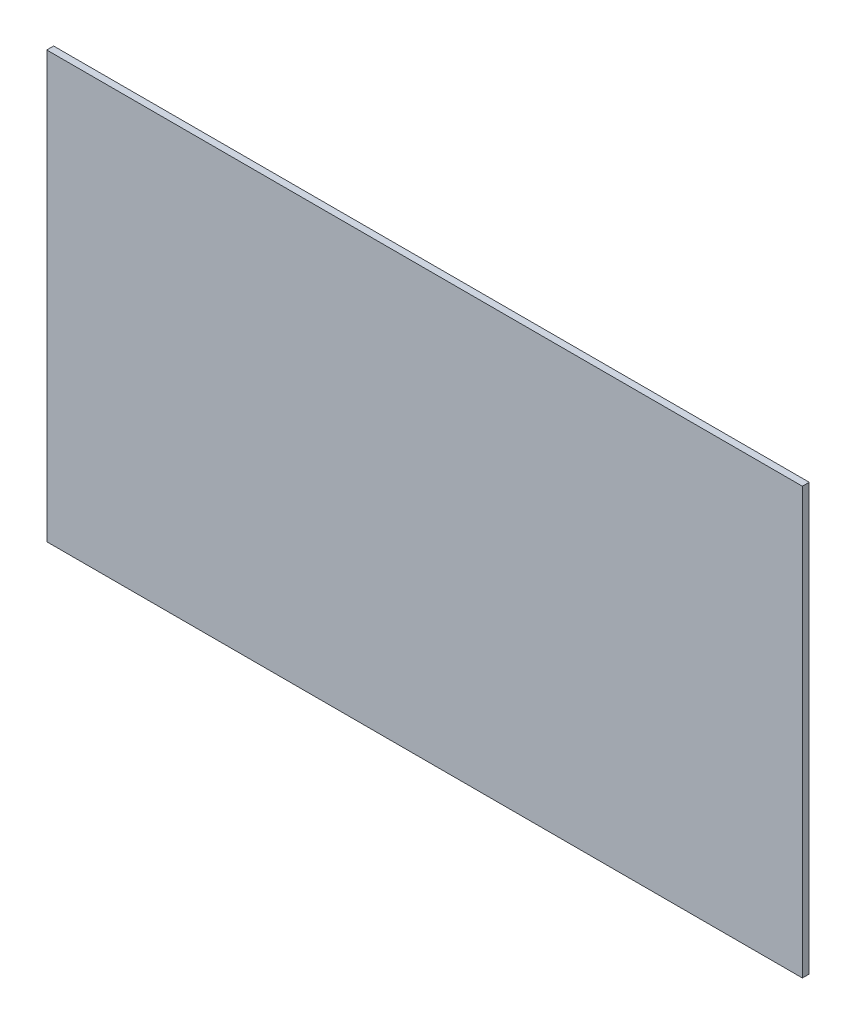
SolidWorks part; units mm, degrees
material "ABS PC"
ref_plane "Front Plane" through (0, 0, 0) normal (0, 0, 1) x (1, 0, 0)
ref_plane "Top Plane" through (0, 0, 0) normal (0, 1, 0) x (1, 0, 0)
ref_plane "Right Plane" through (0, 0, 0) normal (1, 0, 0) x (0, 0, -1)
sketch "Sketch1" plane through (0, 0, 0) normal (0, 0, 1) x (1, 0, 0)
  line L0 (64.8348, 267.2573) -> (78.8048, 267.2573) construction
  line L1 (64.8348, 267.2573) -> (64.8348, 259.3833) construction
  line L2 (78.8048, 259.3833) -> (78.8048, 267.2573) construction
  line L3 (64.8348, 259.3833) -> (78.8048, 259.3833) construction
  line L8 (78.8048, 267.2573) -> (64.8348, 267.2573)
  line L9 (64.8348, 267.2573) -> (64.8348, 259.3833)
  line L10 (64.8348, 259.3833) -> (78.8048, 259.3833)
  line L11 (78.8048, 259.3833) -> (78.8048, 267.2573)
extrude "Boss-Extrude1" add sketch "Sketch1" along normal blind 0.127
